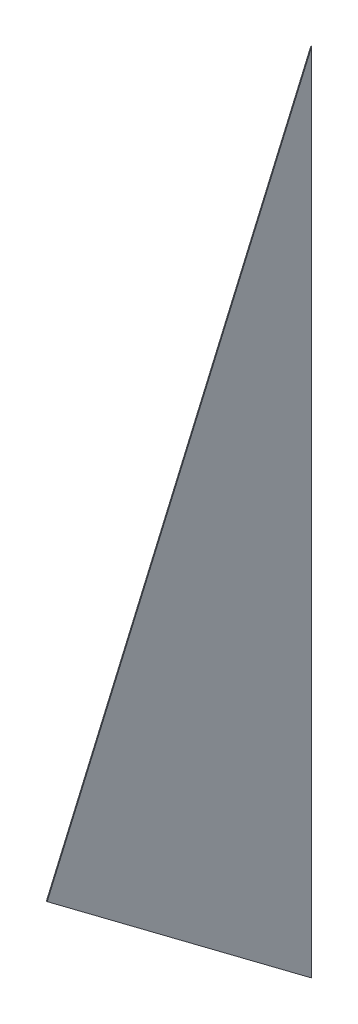
SolidWorks part; units mm, degrees
ref_plane "Front Plane" through (0, 0, 0) normal (0, 0, 1) x (1, 0, 0)
ref_plane "Top Plane" through (0, 0, 0) normal (0, 1, 0) x (1, 0, 0)
ref_plane "Right Plane" through (0, 0, 0) normal (1, 0, 0) x (0, 0, -1)
sketch "Sketch2" plane through (0, 0, 0) normal (1, 0, 0) x (0, 0, -1)
  line L0 (0, 0) -> (1016, 2336.8)
  line L1 (1016, 2336.8) -> (1016, -762)
  line L2 (1016, -762) -> (0, 0)
  dimension "D1" = 1016
  dimension "D2" = 3098.8
  dimension "D3" = 762
extrude "Boss-Extrude1" add sketch "Sketch2" along normal mid plane 3.175
